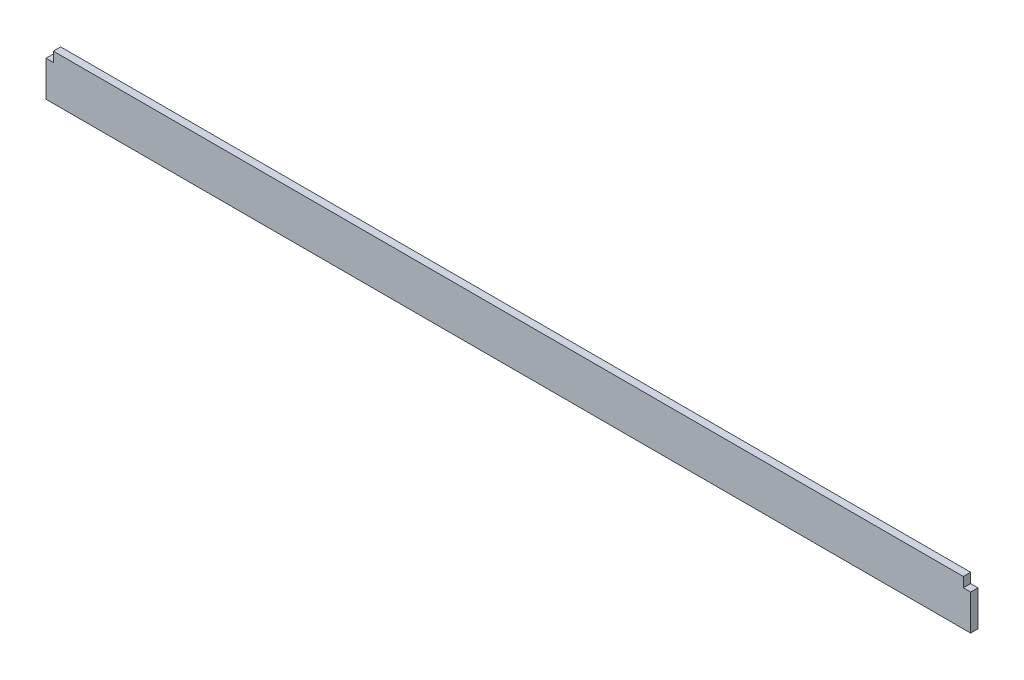
SolidWorks part; units mm, degrees
ref_plane "Front Plane" through (0, 0, 0) normal (0, 0, 1) x (1, 0, 0)
ref_plane "Top Plane" through (0, 0, 0) normal (0, 1, 0) x (1, 0, 0)
ref_plane "Right Plane" through (0, 0, 0) normal (1, 0, 0) x (0, 0, -1)
sketch "Sketch1" plane through (0, 0, 0) normal (0, 0, 1) x (1, 0, 0)
  line L1 (0, 0) -> (4787.9, 0)
  line L2 (0, 0) -> (0, 184.15)
  line L3 (38.1, 234.95) -> (4749.8, 234.95)
  line L4 (4787.9, 0) -> (4787.9, 184.15)
  line L7 (0, 184.15) -> (38.1, 184.15)
  line L8 (38.1, 234.95) -> (38.1, 184.15)
  line L11 (4787.9, 184.15) -> (4749.8, 184.15)
  line L12 (4749.8, 234.95) -> (4749.8, 184.15)
  dimension "D1" = 234.95
  dimension "D2" = 4787.9
  dimension "D3" = 50.8
  dimension "D4" = 38.1
  dimension "D5" = 38.1
  dimension "D6" = 50.8
extrude "Boss-Extrude1" add sketch "Sketch1" along normal blind 38.1
